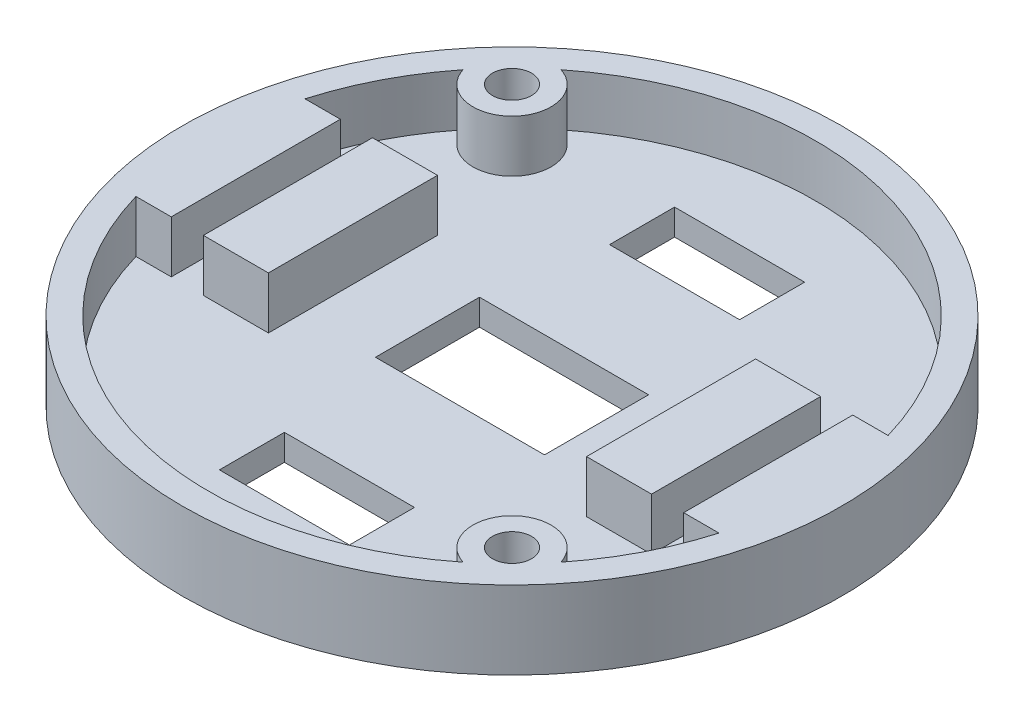
SolidWorks part; units mm, degrees
ref_plane "Front Plane" through (0, 0, 0) normal (0, 0, 1) x (1, 0, 0)
ref_plane "Top Plane" through (0, 0, 0) normal (0, 1, 0) x (1, 0, 0)
ref_plane "Right Plane" through (0, 0, 0) normal (1, 0, 0) x (0, 0, -1)
sketch "Sketch1" plane through (0, 0, 0) normal (0, 1, 0) x (1, 0, 0)
  circle A0 centre (0, 0) radius 25.34
  dimension "D1" = 50.68
extrude "Boss-Extrude1" add sketch "Sketch1" along normal blind 2
sketch "Sketch6" plane through (0, 2, 0) normal (0, 1, 0) x (1, 0, 0)
  circle A0 centre (0, 0) radius 23.34
  circle A1 centre (0, 0) radius 25.34
  circle A2 centre (0, 0) radius 25.34
  dimension "D1" = 0
  dimension "D2" = 2
sketch "Sketch2" plane through (0, 2, 0) normal (0, 1, 0) x (1, 0, 0)
  line L0 (-17.23, 0) -> (17.23, 0) construction
  line L1 (0, 32.0817) -> (0, -28.5676) construction
  line L10 (12.23, -6.5) -> (17.23, -6.5)
  line L11 (12.23, -6.5) -> (12.23, 6.5)
  line L12 (12.23, 6.5) -> (17.23, 6.5)
  line L13 (17.23, -6.5) -> (17.23, 6.5)
  line L26 (22.4166, 6.5) -> (19.7, 6.5)
  line L27 (19.7, 6.5) -> (19.7, -6.5)
  line L32 (19.7, -6.5) -> (22.4166, -6.5)
  line L33 (-19.7, -6.5) -> (-22.4166, -6.5)
  line L34 (-12.23, 6.5) -> (-17.23, 6.5)
  line L35 (-17.23, -6.5) -> (-17.23, 6.5)
  line L36 (-12.23, -6.5) -> (-17.23, -6.5)
  line L37 (-12.23, -6.5) -> (-12.23, 6.5)
  line L38 (-22.4166, 6.5) -> (-19.7, 6.5)
  line L39 (-19.7, 6.5) -> (-19.7, -6.5)
  circle A2 centre (0, 0) radius 23.34 construction
  arc A3 (-22.4166, 6.5) -> (-22.4166, -6.5) centre (0, 0) ccw
  arc A4 (22.4166, -6.5) -> (22.4166, 6.5) centre (0, 0) ccw
  point P2 (0, 0)
  point P7 (17.23, 0)
  dimension "D1" = 2.47
  dimension "D2" = 39.4
  dimension "D3" = 5
  dimension "D4" = 13
extrude "Boss-Extrude2" add sketch "Sketch2" along normal blind 4
sketch "Sketch3" plane through (0, 2, 0) normal (0, 1, 0) x (1, 0, 0)
  line L0 (-15.422, 15.422) -> (15.422, -15.422) construction
  line L1 (-43.7486, 0) -> (48.7139, 0) construction
  circle A0 centre (-15.422, 15.422) radius 1.5
  circle A1 centre (15.422, -15.422) radius 1.5
  point P6 (0, 0)
  dimension "D3" = 3
  dimension "D1" = 45
  dimension "D2" = 43.62
extrude "Cut-Extrude1" cut sketch "Sketch3" against normal through all
sketch "Sketch4" plane through (0, 2, 0) normal (0, 1, 0) x (1, 0, 0)
  line L0 (-60.1037, 0) -> (65.0626, 0) construction
  line L1 (5, 17.5) -> (-5, 17.5)
  line L2 (5, 17.5) -> (5, 12.5)
  line L3 (5, 12.5) -> (-5, 12.5)
  line L4 (-5, 17.5) -> (-5, 12.5)
  line L5 (5, 17.5) -> (-5, 12.5) construction
  line L6 (5, 12.5) -> (-5, 17.5) construction
  line L7 (5, -12.5) -> (-5, -17.5) construction
  line L8 (5, -17.5) -> (-5, -12.5) construction
  line L9 (-5, -17.5) -> (-5, -12.5)
  line L10 (5, -12.5) -> (-5, -12.5)
  line L11 (5, -17.5) -> (5, -12.5)
  line L12 (5, -17.5) -> (-5, -17.5)
  line L14 (6.5, 4) -> (-6.5, 4)
  line L15 (6.5, 4) -> (6.5, -4)
  line L16 (6.5, -4) -> (-6.5, -4)
  line L17 (-6.5, 4) -> (-6.5, -4)
  line L18 (6.5, 4) -> (-6.5, -4) construction
  line L19 (6.5, -4) -> (-6.5, 4) construction
  point P0 (0, 15)
  point P12 (0, -15)
  point P13 (0, 0)
  dimension "D1" = 10
  dimension "D2" = 5
  dimension "D3" = 15
  dimension "D4" = 13
  dimension "D5" = 8
extrude "Cut-Extrude2" cut sketch "Sketch4" against normal through all
sketch "Sketch7" plane through (0, 2, 0) normal (0, 1, 0) x (1, 0, 0)
  arc A0 (18.2805, -14.5114) -> (14.5114, -18.2805) centre (15.422, -15.422) ccw
  arc A1 (-18.2805, 14.5114) -> (-14.5114, 18.2805) centre (-15.422, 15.422) ccw
  circle A2 centre (-15.422, 15.422) radius 1.5 construction
  circle A3 centre (15.422, -15.422) radius 1.5 construction
  circle A4 centre (-15.422, 15.422) radius 1.5
  circle A5 centre (15.422, -15.422) radius 1.5
  arc A6 (-18.2805, 14.5114) -> (14.5114, -18.2805) centre (0, 0) ccw
  circle A7 centre (0, 0) radius 25.34
  circle A8 centre (0, 0) radius 25.34
  circle A9 centre (0, 0) radius 23.34 construction
  arc A10 (18.2805, -14.5114) -> (-14.5114, 18.2805) centre (0, 0) ccw
  dimension "D1" = 6
  dimension "D2" = 0
  dimension "D3" = 2
extrude "Boss-Extrude3" add sketch "Sketch7" along normal up to surface (4 mm away) up to face at (14.73, 6, 0)
